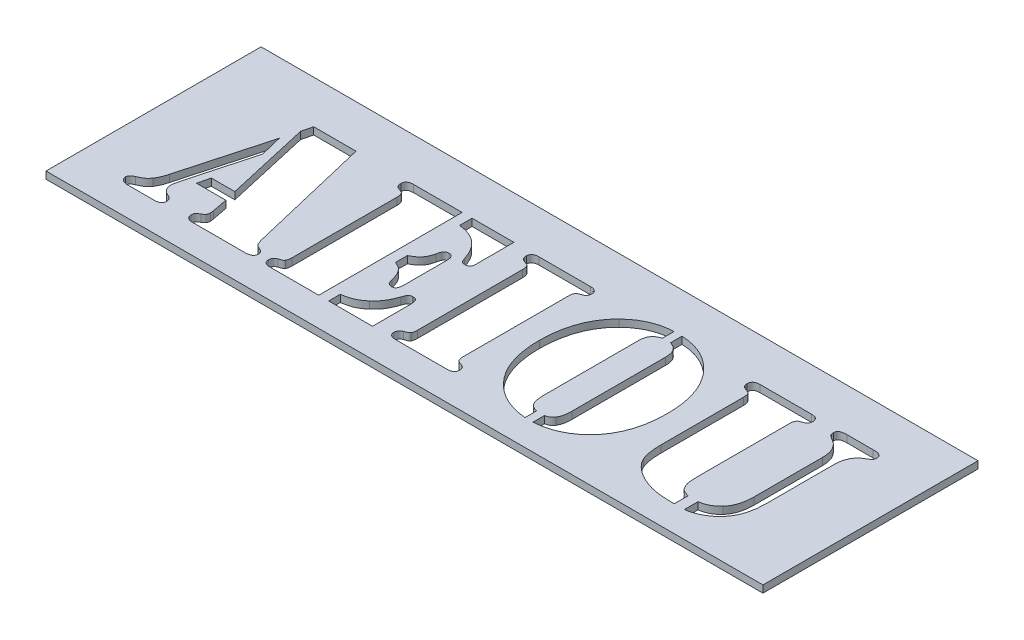
SolidWorks part; units mm, degrees
material "BUTYL"
ref_plane "Front Plane" through (0, 0, 0) normal (0, 0, 1) x (1, 0, 0)
ref_plane "Top Plane" through (0, 0, 0) normal (0, 1, 0) x (1, 0, 0)
ref_plane "Right Plane" through (0, 0, 0) normal (1, 0, 0) x (0, 0, -1)
sketch "Sketch1" plane through (0, 0, 0) normal (0, 1, 0) x (1, 0, 0)
  line L1 (25, 7.5) -> (-25, 7.5)
  line L2 (25, 7.5) -> (25, -7.5)
  line L3 (25, -7.5) -> (-25, -7.5)
  line L4 (-25, 7.5) -> (-25, -7.5)
  line L5 (25, 7.5) -> (-25, -7.5) construction
  line L6 (25, -7.5) -> (-25, 7.5) construction
  point P0 (0, 0)
  dimension "D1" = 50
  dimension "D2" = 15
extrude "Boss-Extrude1" add sketch "Sketch1" along normal blind 0.5
sketch "Sketch2" plane through (0, 0.5, 0) normal (0, 1, 0) x (1, 0, 0)
  line L0 (-25, -5.493) -> (25, -5.493) construction
  line L1 (-25, 7.5) -> (-25, -7.5) construction
  line L2 (25, -7.5) -> (25, 7.5) construction
  text T0 "AEIOU" font "Stencil" height 10
extrude "Cut-Extrude1" cut sketch "Sketch2" against normal up to next
